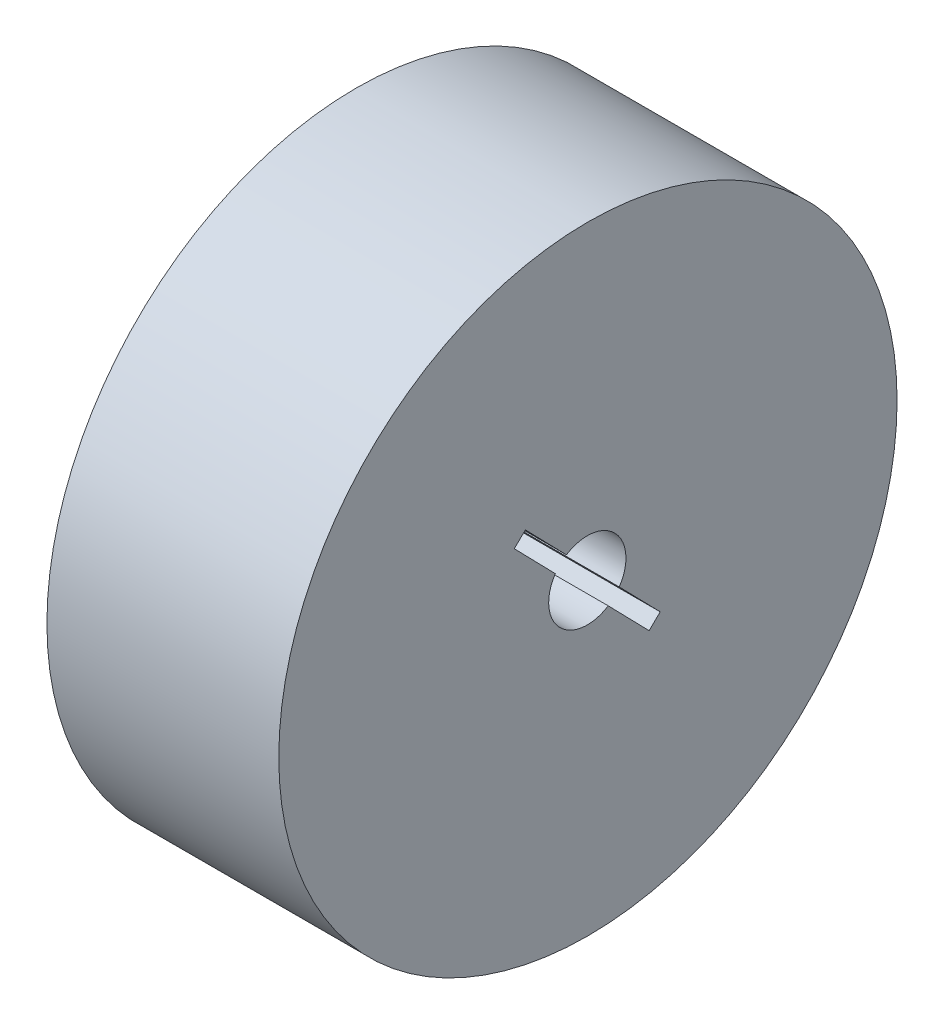
SolidWorks part; units mm, degrees
ref_plane "前视基准面" through (0, 0, 0) normal (0, 0, 1) x (1, 0, 0)
ref_plane "上视基准面" through (0, 0, 0) normal (0, 1, 0) x (1, 0, 0)
ref_plane "右视基准面" through (0, 0, 0) normal (1, 0, 0) x (0, 0, -1)
sketch "草图1" plane through (0, 0, 0) normal (1, 0, 0) x (0, 0, -1)
  circle A0 centre (0, 0) radius 40
  dimension "D1" = 80
extrude "凸台-拉伸1" add sketch "草图1" along normal blind 30
sketch "草图2" plane through (0, 0, 0) normal (1, 0, 0) x (0, 0, -1)
  line L0 (2.6235, -4.3213) -> (7.9186, -9.7561)
  line L3 (-2.7814, 4.0922) -> (-8.095, 9.5459)
  line L4 (-8.095, 9.5459) -> (-9.5275, 8.1502)
  line L5 (-9.5275, 8.1502) -> (-4.2142, 2.6968)
  line L6 (7.9186, -9.7561) -> (9.3511, -8.3604)
  line L7 (9.3511, -8.3604) -> (4.0557, -2.9253)
  arc A0 (4.0557, -2.9253) -> (-2.7814, 4.0922) centre (-0.0799, -0.1152) ccw
  arc A1 (-4.2142, 2.6968) -> (2.6235, -4.3213) centre (-0.0799, -0.1152) ccw
  dimension "D1" = 10
  dimension "D2" = 2
  dimension "D3" = 2
  dimension "D4" = 25
  dimension "D7" = 25
extrude "切除-拉伸1" cut sketch "草图2" along normal through all
